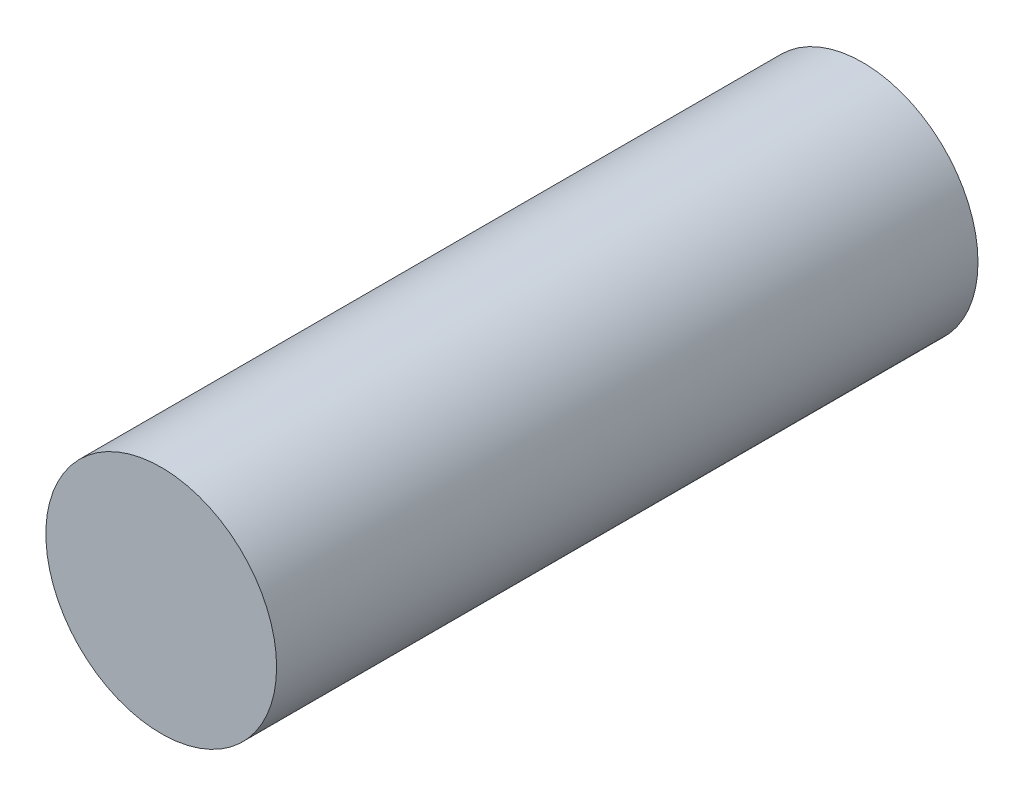
SolidWorks part; units mm, degrees
ref_plane "Plan de face" through (0, 0, 0) normal (0, 0, 1) x (1, 0, 0)
ref_plane "Plan de dessus" through (0, 0, 0) normal (0, 1, 0) x (1, 0, 0)
ref_plane "Plan de droite" through (0, 0, 0) normal (1, 0, 0) x (0, 0, -1)
sketch "Esquisse1" plane through (0, 0, 0) normal (0, 0, 1) x (1, 0, 0)
  circle A0 centre (0, 0) radius 5.05
  dimension "D1" = 10.1
extrude "Boss.-Extru.1" add sketch "Esquisse1" along normal blind 30.7
sketch "Esquisse2" plane through (0, 0, 0) normal (0, 0, -1) x (-1, 0, 0)
  circle A0 centre (0, 0) radius 2.05
  dimension "D1" = 4.1
extrude "Enlèv. mat.-Extru.1" cut sketch "Esquisse2" against normal blind 2.65
